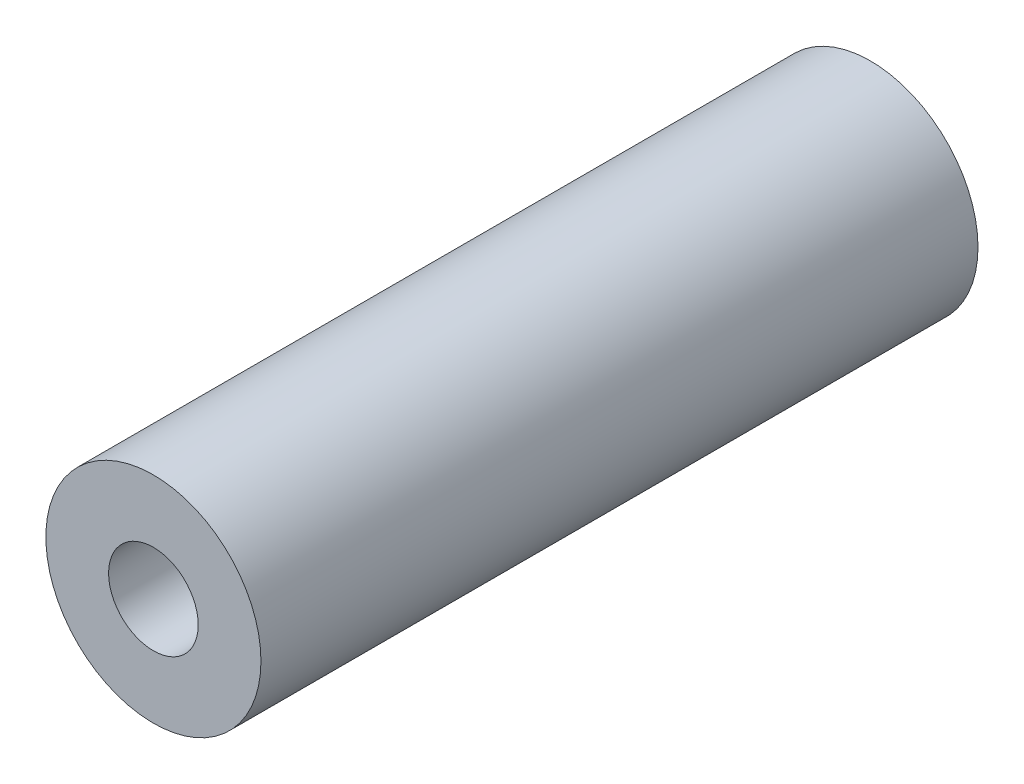
SolidWorks part; units mm, degrees
ref_plane "正面" through (0, 0, 0) normal (0, 0, 1) x (1, 0, 0)
ref_plane "平面" through (0, 0, 0) normal (0, 1, 0) x (1, 0, 0)
ref_plane "右側面" through (0, 0, 0) normal (1, 0, 0) x (0, 0, -1)
sketch "ｽｹｯﾁ1" plane through (0, 0, 0) normal (0, 0, 1) x (1, 0, 0)
  circle A0 centre (0, 0) radius 3
  dimension "D1" = 6
extrude "ﾎﾞｽ - 押し出し1" add sketch "ｽｹｯﾁ1" along normal mid plane 20
hole_wizard "M3x0.5 ねじ穴1" positions "3Dｽｹｯﾁ1" profile "ｽｹｯﾁ2" tap size "M3x0.5" standard "JIS"
sketch3d "3Dｽｹｯﾁ1"
  line L0 (0, 0, 10) -> (0, 0, -10) construction
  point P0 (0, 0, 10)
  point P4 (0, 0, -10)
sketch "ｽｹｯﾁ2" plane through (0, 0, 10) normal (1, 0, 0) x (0, -1, 0)
  line L0 (0, 0) -> (0, 7.2511)
  line L1 (0, 7.2511) -> (1.25, 6.5)
  line L2 (1.25, 6.5) -> (1.25, 0)
  line L5 (1.25, 0) -> (0, 0)
  line L10 (0, 7.2511) -> (-1.25, 6.5) construction
  line L11 (0, -6.35) -> (0, 107.95) construction
  dimension "ねじ下穴ﾄﾞﾘﾙ直径" = 2.5
  dimension "ねじ下穴ﾄﾞﾘﾙの深さ" = 6.5
  dimension "ﾄﾞﾘﾙ角度" = 118
cosmetic thread "穴のねじ山1"
cosmetic thread "穴のねじ山2"
sketch "ｽｹｯﾁ3" plane through (0, 0, -10) normal (0, 0, -1) x (-1, 0, 0)
  circle A0 centre (0, 0) radius 1.25
extrude "ｶｯﾄ - 押し出し1" cut sketch "ｽｹｯﾁ3" against normal blind 20
